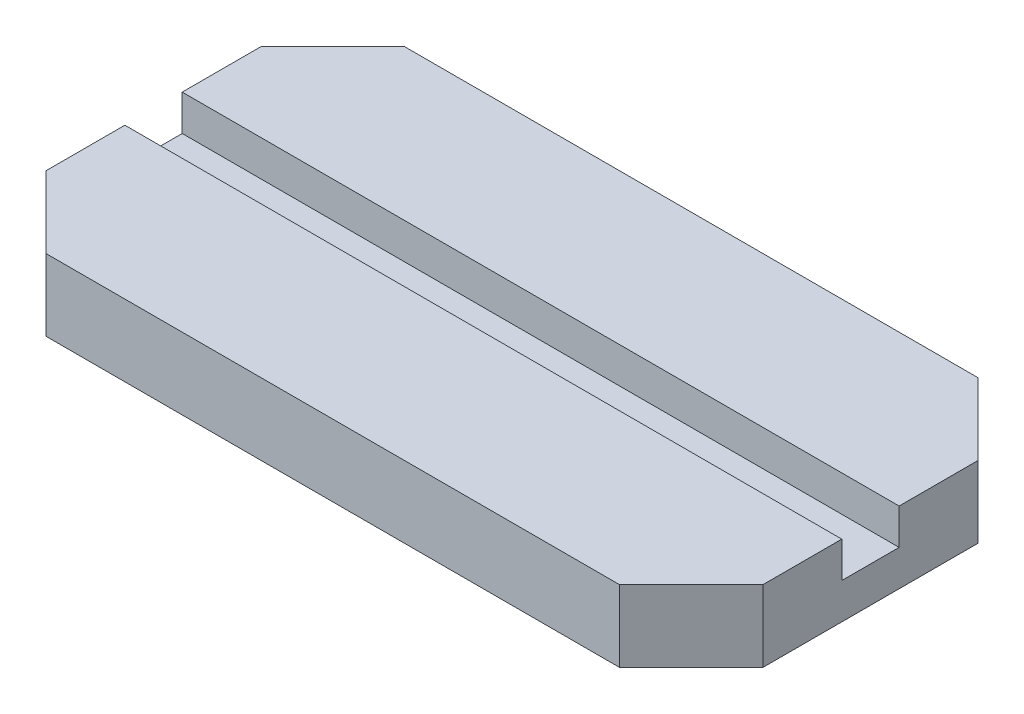
SolidWorks part; units mm, degrees
ref_plane "Front Plane" through (0, 0, 0) normal (0, 0, 1) x (1, 0, 0)
ref_plane "Top Plane" through (0, 0, 0) normal (0, 1, 0) x (1, 0, 0)
ref_plane "Right Plane" through (0, 0, 0) normal (1, 0, 0) x (0, 0, -1)
sketch "Sketch1" plane through (0, 0, 0) normal (0, 1, 0) x (1, 0, 0)
  line L1 (-50, 25) -> (50, 25)
  line L2 (-50, 25) -> (-50, -25)
  line L3 (-50, -25) -> (50, -25)
  line L4 (50, 25) -> (50, -25)
  dimension "D1" = 50
  dimension "D2" = 100
  dimension "D3" = 50
  dimension "D4" = 25
extrude "Boss-Extrude1" add sketch "Sketch1" along normal blind 10
chamfer "Chamfer1" distance 10 angle 45 4 edges at (-50, 5, -25) (-50, 5, 25) (50, 5, -25) (50, 5, 25)
sketch "Sketch2" plane through (0, 10, 0) normal (0, 1, 0) x (1, 0, 0)
  line L1 (-58.3808, 4) -> (54.7849, 4)
  line L2 (-58.3808, 4) -> (-58.3808, -4)
  line L3 (-58.3808, -4) -> (54.7849, -4)
  line L4 (54.7849, 4) -> (54.7849, -4)
  dimension "D1" = 4
  dimension "D2" = 8
extrude "Cut-Extrude1" cut sketch "Sketch2" against normal blind 5
